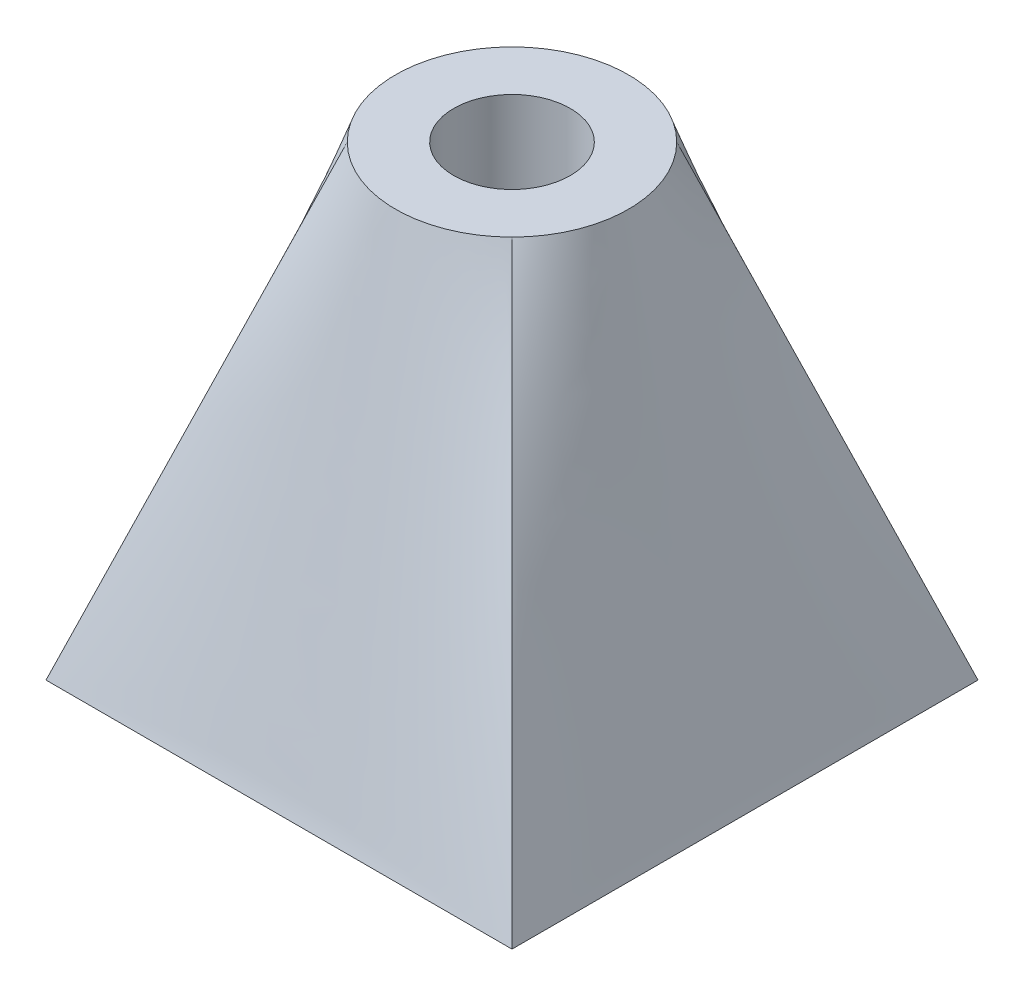
SolidWorks part; units mm, degrees
ref_plane "Front Plane" through (0, 0, 0) normal (0, 0, 1) x (1, 0, 0)
ref_plane "Top Plane" through (0, 0, 0) normal (0, 1, 0) x (1, 0, 0)
ref_plane "Right Plane" through (0, 0, 0) normal (1, 0, 0) x (0, 0, -1)
sketch "Sketch1" plane through (0, 0, 0) normal (0, 1, 0) x (1, 0, 0)
  line L1 (0, 0) -> (40, 0)
  line L2 (0, 0) -> (0, 40)
  line L3 (0, 40) -> (40, 40)
  line L4 (40, 0) -> (40, 40)
  dimension "D1" = 40
ref_plane "Plane1" through (0, 40, 0) normal (0, 1, 0) x (1, 0, 0)
sketch "Sketch2" plane through (0, 40, 0) normal (0, 1, 0) x (1, 0, 0)
  line L0 (0, 20) -> (40, 20) construction
  line L1 (0, 0) -> (0, 40) construction
  line L2 (40, 0) -> (40, 40) construction
  line L3 (20, 40) -> (20, 0) construction
  line L4 (0, 40) -> (40, 40) construction
  line L5 (0, 0) -> (40, 0) construction
  circle A0 centre (20, 20) radius 10
loft "Loft1" add profiles "Sketch1", "Sketch2"
sketch "Sketch3" plane through (0, 40, 0) normal (0, 1, 0) x (1, 0, 0)
  circle A0 centre (20, 20) radius 5
  dimension "D1" = 10
extrude "Cut-Extrude1" cut sketch "Sketch3" against normal through all
